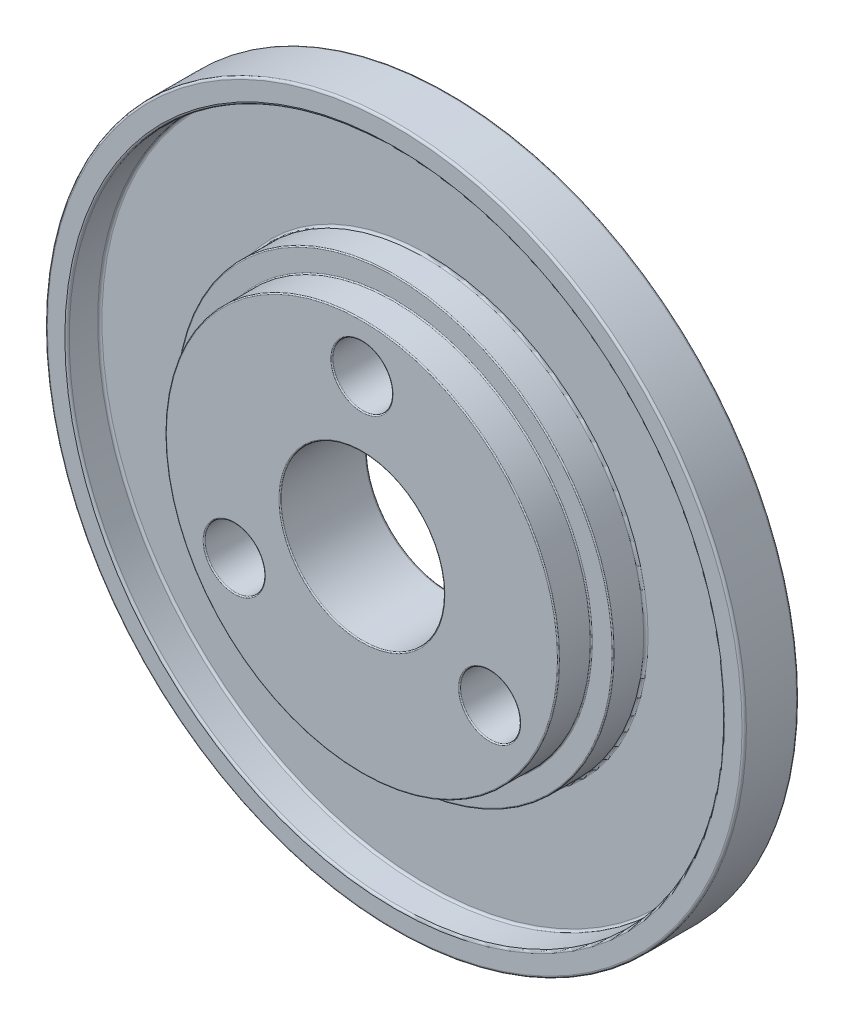
SolidWorks part; units mm, degrees
ref_plane "Alzado" through (0, 0, 0) normal (0, 0, 1) x (1, 0, 0)
ref_plane "Planta" through (0, 0, 0) normal (0, 1, 0) x (1, 0, 0)
ref_plane "Vista lateral" through (0, 0, 0) normal (1, 0, 0) x (0, 0, -1)
sketch "Croquis1" plane through (0, 0, 0) normal (0, 0, 1) x (1, 0, 0)
  circle A0 centre (0, 0) radius 32
  circle A1 centre (0, 0) radius 7.5
  dimension "D1" = 64
  dimension "D2" = 15
extrude "Saliente-Extruir1" add sketch "Croquis1" along normal blind 5
sketch "Croquis2" plane through (0, 0, 5) normal (0, 0, 1) x (1, 0, 0)
  circle A0 centre (0, 0) radius 30
  circle A1 centre (0, 0) radius 20
  dimension "D1" = 60
  dimension "D2" = 40
extrude "Cortar-Extruir1" cut sketch "Croquis2" against normal blind 3
fillet "Redondeo1" radius 0.2 6 edges at (30, 0, 2) (20, 0, 2) (32, 0, 5) (30, 0, 5) (7.5, 0, 0) (32, 0, 0)
sketch "Croquis14" plane through (0, 0, 5) normal (0, 0, 1) x (1, 0, 0)
  circle A0 centre (0, 0) radius 18
  circle A1 centre (0, 0) radius 7.5 construction
  circle A2 centre (0, 0) radius 7.5
  dimension "D1" = 36
extrude "Saliente-Extruir4" add sketch "Croquis14" along normal blind 3
sketch "Croquis18" plane through (0, 0, 8) normal (0, 0, 1) x (1, 0, 0)
  circle A0 centre (0, 0) radius 13.5
  circle A1 centre (0, 13.5) radius 2.75
  circle A2 centre (11.6913, -6.75) radius 2.75
  circle A3 centre (-11.6913, -6.75) radius 2.75
  point P12 (0, 0)
  dimension "D1" = 27
  dimension "D2" = 5.5
  dimension "D3" = 3
extrude "Cortar-Extruir6" cut sketch "Croquis18" against normal up to surface (8 mm away) contours A1 | A3 | A2 up to face at (7.7, 0, 0)
hole_wizard "Refrentado para tornillo tapón con cabeza plana de clavija de M54" positions "Croquis3D6" profile "Croquis19" countersink size "M5" standard "Ansi Metric" end condition through all
sketch3d "Croquis3D6"
  line L0 (11.6913, -6.75, 0) -> (11.6913, -6.75, 8) construction
  line L1 (-11.6913, -6.75, 0) -> (-11.6913, -6.75, 8) construction
  line L2 (0, 13.5, 0) -> (0, 13.5, 8) construction
  point P0 (11.6913, -6.75, 0)
  point P4 (-11.6913, -6.75, 0)
  point P8 (0, 13.5, 0)
sketch "Croquis19" plane through (11.6913, -6.75, 0) normal (1, 0, 0) x (0, 1, 0)
  line L0 (0, 0) -> (0, 8)
  line L1 (0, 8) -> (2.75, 8)
  line L2 (2.75, 8) -> (2.75, 2.85)
  line L3 (2.75, 2.85) -> (5.6, 0)
  line L5 (5.6, 0) -> (0, 0)
  line L6 (-2.75, 2.85) -> (-5.6, 0) construction
  line L11 (0, -6.35) -> (0, 107.95) construction
  dimension "Diámetro de taladro hasta el siguiente" = 5.5
  dimension "Profundidad de taladro hasta el siguiente" = 8
  dimension "Diámetro de avellanado cercano" = 11.2
  dimension "Ángulo de avellanado cercano" = 90
fillet "Redondeo3" radius 0.1 7 edges at (20, 0, 5) (18, 0, 5) (18, 0, 8) (-8.9413, -6.75, 8) (2.75, 13.5, 8) (14.4413, -6.75, 8) (7.5, 0, 8)
